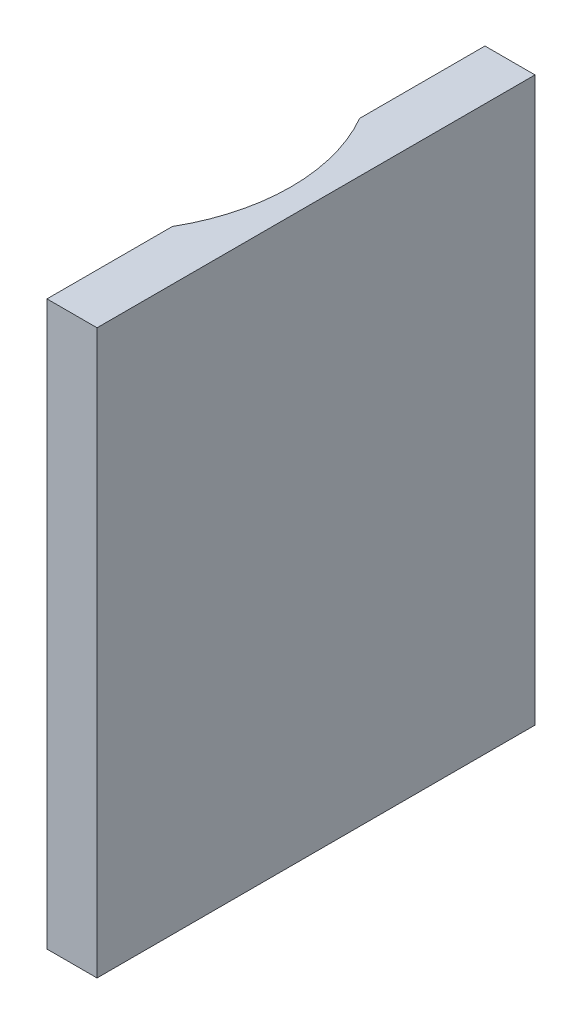
SolidWorks part; units mm, degrees
ref_plane "Alzado" through (0, 0, 0) normal (0, 0, 1) x (1, 0, 0)
ref_plane "Planta" through (0, 0, 0) normal (0, 1, 0) x (1, 0, 0)
ref_plane "Vista lateral" through (0, 0, 0) normal (1, 0, 0) x (0, 0, -1)
sketch "Croquis1" plane through (0, 0, 0) normal (0, 1, 0) x (1, 0, 0)
  line L0 (13, 17.5) -> (13, 7.4833)
  line L1 (13, 17.5) -> (17, 17.5)
  line L3 (13, -17.5) -> (17, -17.5)
  line L4 (17, 17.5) -> (17, -17.5)
  line L5 (-17, 17.5) -> (0, 0) construction
  line L6 (-17, -17.5) -> (0, 0) construction
  line L7 (13, 13.3824) -> (17, 17.5) construction
  line L8 (10.4518, -10.7592) -> (17, -17.5) construction
  line L9 (13, -7.4833) -> (13, -17.5)
  arc A1 (13, -7.4833) -> (13, 7.4833) centre (0, 0) ccw
  dimension "D3" = 4
  dimension "D4" = 35
extrude "Saliente-Extruir1" add sketch "Croquis1" along normal blind 45
